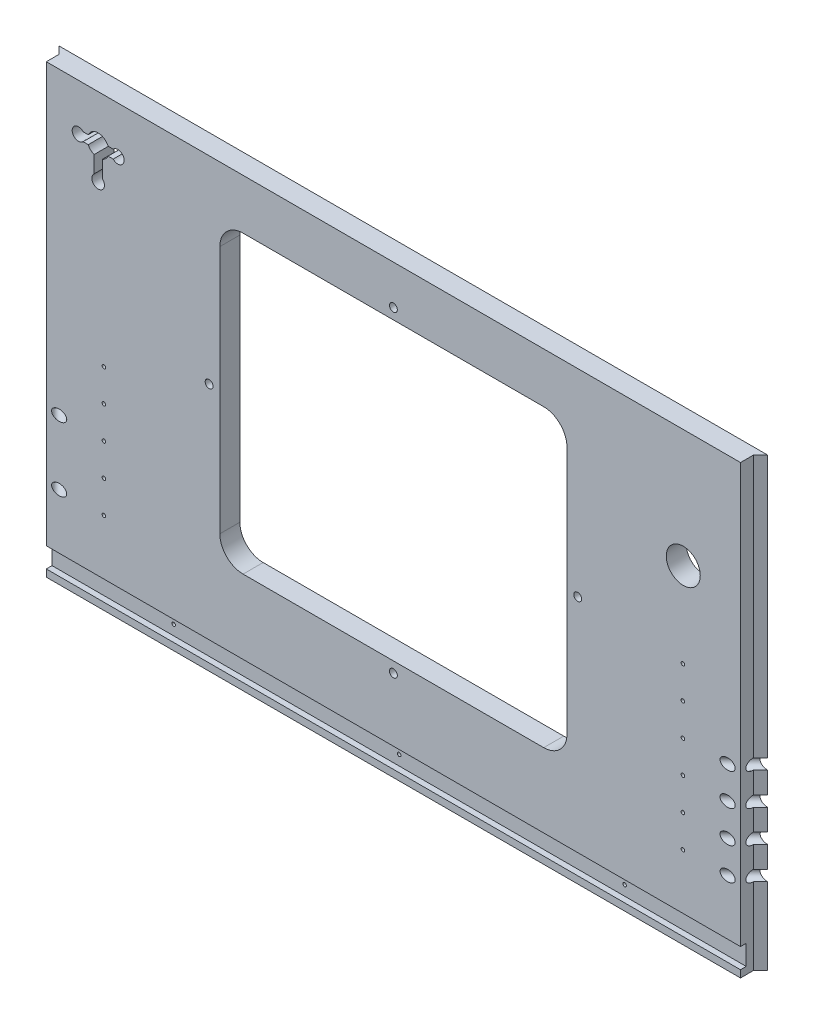
SolidWorks part; units mm, degrees
material "Maple"
ref_plane "Front Plane" through (0, 0, 0) normal (0, 0, 1) x (1, 0, 0)
ref_plane "Top Plane" through (0, 0, 0) normal (0, 1, 0) x (1, 0, 0)
ref_plane "Right Plane" through (0, 0, 0) normal (1, 0, 0) x (0, 0, -1)
sketch "Sketch1" plane through (0, 0, 0) normal (0, 0, 1) x (1, 0, 0)
  line L0 (8932.6508, -5243.5125) -> (10226.1458, -5243.5125)
  line L1 (9086.3208, -4722.0918) -> (10222.9708, -4853.7812)
  line L2 (8914.8708, -6342.0625) -> (10197.5708, -6342.0625)
  line L3 (8914.8708, -5808.6625) -> (10197.5708, -5808.6625)
  line L4 (8919.6333, -5253.0375) -> (10218.2083, -5253.0375)
  line L5 (9134.2633, -4656.1375) -> (9134.2633, -4638.3575)
  line L6 (9091.0833, -4638.3575) -> (9134.2633, -4638.3575)
  line L7 (9091.0833, -4567.2375) -> (9091.0833, -4638.3575)
  line L8 (9134.2633, -4656.1375) -> (9581.3033, -4656.1375)
  line L9 (9091.0833, -4567.2375) -> (9624.4833, -4567.2375)
  line L10 (9581.3033, -4656.1375) -> (9581.3033, -4638.3575)
  line L11 (9581.3033, -4638.3575) -> (9624.4833, -4638.3575)
  line L12 (9624.4833, -4567.2375) -> (9624.4833, -4638.3575)
  line L13 (8932.6508, -5225.7325) -> (9344.9775, -5225.7325)
  line L14 (8932.6508, -5256.2125) -> (8932.6508, -5243.5125)
  line L15 (8911.6958, -5256.2125) -> (8932.6508, -5256.2125)
  line L16 (8914.8708, -4722.0918) -> (9086.3208, -4722.0918)
  line L17 (8911.6958, -4715.5913) -> (8932.6508, -4715.5913)
  line L18 (8914.8708, -6342.0625) -> (8914.8708, -5808.6625)
  line L19 (12082.9917, -4722.0918) -> (10946.3417, -4853.7812)
  line L20 (12236.6617, -5243.5125) -> (10943.1667, -5243.5125)
  line L21 (10951.1042, -5253.0375) -> (12249.6792, -5253.0375)
  line L22 (10838.3917, -5656.2625) -> (11308.2917, -5656.2625)
  line L23 (10838.3917, -5719.7625) -> (11308.2917, -5719.7625)
  line L24 (10838.3917, -5742.5368) -> (11308.2917, -5742.5368)
  line L25 (10806.6417, -6342.0625) -> (11340.0417, -6342.0625)
  line L26 (10803.4667, -6335.7125) -> (11343.2167, -6335.7125)
  line L27 (10803.4667, -6317.9325) -> (11343.2167, -6317.9325)
  line L28 (10943.1667, -5225.7325) -> (11376.4483, -5225.7325)
  line L29 (11506.7292, -4754.5625) -> (10806.6417, -4827.5875)
  line L30 (11506.7292, -4567.2375) -> (11506.7292, -4754.5625)
  line L31 (10806.6417, -4567.2375) -> (10806.6417, -4827.5875)
  line L32 (10806.6417, -4567.2375) -> (11506.7292, -4567.2375)
  line L33 (10235.6708, -6329.3625) -> (10245.1958, -6329.3625)
  line L34 (10245.1958, -6329.3625) -> (10254.7208, -6278.5625)
  line L35 (10302.3458, -6329.3625) -> (10311.8708, -6278.5625)
  line L36 (10302.3458, -6329.3625) -> (10292.8208, -6329.3625)
  line L37 (10245.1958, -5821.3625) -> (10254.7208, -5872.1625)
  line L38 (10235.6708, -5821.3625) -> (10245.1958, -5821.3625)
  line L39 (10292.8208, -5821.3625) -> (10302.3458, -5821.3625)
  line L40 (10302.3458, -5821.3625) -> (10311.8708, -5872.1625)
  line L41 (10235.6708, -5821.3625) -> (10235.6708, -6329.3625)
  line L42 (10254.7208, -5872.1625) -> (10254.7208, -6278.5625)
  line L43 (10311.8708, -5872.1625) -> (10311.8708, -6278.5625)
  line L44 (10292.8208, -5821.3625) -> (10292.8208, -6329.3625)
  line L45 (8932.6508, -5225.7325) -> (8932.6508, -4715.5913)
  line L46 (8911.6958, -4715.5913) -> (8911.6958, -5256.2125)
  line L47 (8914.8708, -5248.275) -> (8914.8708, -4722.0918)
  line L48 (8919.6333, -5253.0375) -> (8914.8708, -5248.275)
  line L49 (8914.8708, -5145.0875) -> (8937.426, -5145.0875)
  line L50 (8914.8708, -5202.2375) -> (8937.426, -5202.2375)
  line L51 (10838.3917, -5656.2625) -> (10838.3917, -5719.7625)
  line L52 (10832.0417, -5736.1868) -> (10856.1717, -5736.1868)
  line L53 (10806.6417, -6342.0625) -> (10806.6417, -5818.7368)
  line L54 (10832.0417, -5649.9125) -> (10856.1717, -5649.9125)
  line L55 (10832.0417, -5726.1125) -> (10856.1717, -5726.1125)
  line L56 (10806.6417, -5818.7368) -> (10833.9015, -5818.7368)
  line L57 (10832.0417, -5806.0442) -> (10851.6815, -5806.0442)
  line L58 (10856.1717, -5801.5541) -> (10856.1717, -5736.1868)
  line L59 (10838.3917, -5814.2467) -> (10838.3917, -5742.5368)
  line L60 (10832.0417, -5806.0442) -> (10832.0417, -5736.1868)
  line L61 (10803.4667, -6317.9325) -> (10803.4667, -6335.7125)
  line L62 (10197.5708, -5808.6625) -> (10197.5708, -6342.0625)
  line L63 (9762.3842, -6348.4125) -> (9762.3842, -5802.3125)
  line L64 (9780.1642, -6348.4125) -> (9762.3842, -6348.4125)
  line L65 (9780.1642, -5802.3125) -> (9780.1642, -6348.4125)
  line L66 (9762.3842, -5802.3125) -> (9780.1642, -5802.3125)
  line L67 (9332.2775, -6348.4125) -> (9332.2775, -5802.3125)
  line L68 (9332.2775, -6348.4125) -> (9350.0575, -6348.4125)
  line L69 (9350.0575, -5802.3125) -> (9350.0575, -6348.4125)
  line L70 (9332.2775, -5802.3125) -> (9350.0575, -5802.3125)
  line L71 (9993.8374, -6061.075) -> (9993.8374, -6045.2418)
  line L72 (9998.5999, -6065.8375) -> (10014.4331, -6065.8375)
  line L73 (9998.5999, -6084.8875) -> (10014.4331, -6084.8875)
  line L74 (9993.8374, -6105.4832) -> (9993.8374, -6089.65)
  line L75 (9974.7874, -6105.4832) -> (9974.7874, -6089.65)
  line L76 (9954.1917, -6084.8875) -> (9970.0249, -6084.8875)
  line L77 (9974.7874, -6061.075) -> (9974.7874, -6045.2418)
  line L78 (9954.1917, -6065.8375) -> (9970.0249, -6065.8375)
  line L79 (10793.9417, -6237.2875) -> (10816.4969, -6237.2875)
  line L80 (10793.9417, -6294.4375) -> (10816.4969, -6294.4375)
  line L81 (10856.1717, -5649.9125) -> (10856.1717, -5726.1125)
  line L82 (10832.0417, -5726.1125) -> (10832.0417, -5649.9125)
  line L83 (10226.1458, -5225.7325) -> (10226.1458, -5243.5125)
  line L84 (10205.1908, -5257.8) -> (10205.1908, -4844.2499)
  line L85 (10230.9083, -4844.2499) -> (10230.9083, -5257.8)
  line L86 (10205.1908, -5257.8) -> (10230.9083, -5257.8)
  line L87 (10205.1908, -4844.2499) -> (10230.9083, -4844.2499)
  line L88 (10946.3417, -5176.8375) -> (10968.8969, -5176.8375)
  line L89 (9349.4676, -5141.9125) -> (9358.2674, -5141.9125)
  line L90 (10946.3417, -5119.6875) -> (10968.8969, -5119.6875)
  line L91 (9929.011, -4660.9635) -> (10066.0807, -4660.9635)
  line L92 (9929.011, -4678.7435) -> (10066.0807, -4678.7435)
  line L93 (10943.1667, -5225.7325) -> (10943.1667, -5243.5125)
  line L94 (10946.3417, -5248.275) -> (10951.1042, -5253.0375)
  line L95 (10946.3417, -5257.8063) -> (10946.3417, -4849.0188)
  line L96 (10964.1217, -5257.8) -> (10964.1217, -4844.2499)
  line L97 (10938.4042, -4844.2499) -> (10938.4042, -5257.8)
  line L98 (10938.4042, -5257.8) -> (10964.1217, -5257.8)
  line L99 (10964.1217, -4844.2499) -> (10938.4042, -4844.2499)
  line L100 (10344.8908, -4560.8875) -> (10369.0208, -4560.8875)
  line L101 (10344.8908, -4560.8875) -> (10369.0208, -4560.8875)
  line L102 (10800.2917, -4560.8875) -> (10824.4217, -4560.8875)
  line L103 (10200.4156, -5119.6875) -> (10222.9708, -5119.6875)
  line L104 (10200.4156, -5176.8375) -> (10222.9708, -5176.8375)
  line L105 (9344.9775, -5146.4026) -> (9344.9775, -5225.7325)
  line L106 (10344.8908, -4560.8875) -> (10344.8908, -4833.9375)
  line L107 (9792.8642, -5225.7325) -> (9792.8642, -5146.4026)
  line L108 (9362.7575, -5225.7325) -> (9775.0842, -5225.7325)
  line L109 (9680.3633, -4761.8396) -> (9680.3633, -4559.9604)
  line L110 (9656.2333, -4559.9604) -> (9680.3633, -4559.9604)
  line L111 (9656.2333, -4761.8396) -> (9680.3633, -4761.8396)
  line L112 (9656.2333, -4761.8396) -> (9656.2333, -4559.9604)
  line L113 (9779.5743, -5141.9125) -> (9788.374, -5141.9125)
  line L114 (10070.5708, -4665.4536) -> (10070.5708, -4674.2534)
  line L115 (9924.5208, -4674.2534) -> (9924.5208, -4665.4536)
  line L116 (12127.4417, -6188.3925) -> (12205.5015, -6188.3925)
  line L117 (12209.9917, -6170.6125) -> (12209.9917, -6183.9024)
  line L118 (9792.8642, -5225.7325) -> (10226.1458, -5225.7325)
  line L119 (9662.5833, -4754.5625) -> (10362.6708, -4827.5875)
  line L120 (9662.5833, -4567.2375) -> (9662.5833, -4754.5625)
  line L121 (10362.6708, -4567.2375) -> (10362.6708, -4827.5875)
  line L122 (9662.5833, -4567.2375) -> (10362.6708, -4567.2375)
  line L123 (10824.4217, -4833.9375) -> (10800.2917, -4833.9375)
  line L124 (10800.2917, -4833.9375) -> (10800.2917, -4560.8875)
  line L125 (10824.4217, -4560.8875) -> (10824.4217, -4833.9375)
  line L126 (10344.8908, -4833.9375) -> (10369.0208, -4833.9375)
  line L127 (10369.0208, -4833.9375) -> (10369.0208, -4560.8875)
  line L128 (10222.9708, -5248.275) -> (10218.2083, -5253.0375)
  line L129 (10222.9708, -5257.8063) -> (10222.9708, -4849.0188)
  line L130 (11734.6544, -5701.375) -> (11739.2301, -5701.375)
  line L131 (9362.7575, -5225.7325) -> (9362.7575, -5146.4026)
  line L132 (9775.0842, -5146.4026) -> (9775.0842, -5225.7325)
  line L133 (11761.3864, -5701.375) -> (11756.8282, -5701.375)
  line L134 (11734.6544, -5693.755) -> (11739.2301, -5693.755)
  line L135 (11761.4039, -5693.755) -> (11756.8282, -5693.755)
  line L136 (11734.6544, -5701.375) -> (11739.2301, -5701.375)
  line L137 (11744.3462, -5721.3024) -> (11744.3462, -5706.4179)
  line L138 (11751.7122, -5721.3024) -> (11751.7122, -5706.4179)
  line L139 (11740.0917, -6170.6125) -> (11740.0917, -6183.9024)
  line L140 (11689.2917, -6188.3925) -> (11822.6417, -6188.3925)
  line L141 (11689.2917, -6348.4093) -> (11689.2917, -6164.2657)
  line L142 (11689.2917, -6164.2657) -> (11746.4417, -6164.2657)
  line L143 (11746.4417, -6164.2657) -> (11746.4417, -6188.3925)
  line L144 (11689.2917, -6164.2657) -> (11746.4417, -6164.2657)
  line L145 (11340.0417, -5818.7368) -> (11340.0417, -6342.0625)
  line L146 (11290.5117, -5726.1125) -> (11314.6417, -5726.1125)
  line L147 (11290.5117, -5649.9125) -> (11290.5117, -5726.1125)
  line L148 (11340.0417, -5818.7368) -> (11312.7818, -5818.7368)
  line L149 (11314.6417, -5806.0442) -> (11295.0018, -5806.0442)
  line L150 (11290.5117, -5801.5541) -> (11290.5117, -5736.1868)
  line L151 (11308.2917, -5814.2467) -> (11308.2917, -5742.5368)
  line L152 (11314.6417, -5806.0442) -> (11314.6417, -5736.1868)
  line L153 (11290.5117, -5736.1868) -> (11314.6417, -5736.1868)
  line L154 (11848.0417, -6267.1325) -> (11962.3417, -6267.1325)
  line L155 (11962.3417, -6267.1325) -> (11962.3417, -6203.6325)
  line L156 (11343.2167, -6317.9325) -> (11343.2167, -6335.7125)
  line L157 (11365.4417, -5656.2625) -> (11365.4417, -5719.7625)
  line L158 (11365.4417, -5656.2625) -> (11479.7417, -5656.2625)
  line L159 (11778.1917, -6071.3937) -> (11802.3217, -6071.3937)
  line L160 (11314.6417, -5726.1125) -> (11314.6417, -5649.9125)
  line L161 (11314.6417, -5649.9125) -> (11290.5117, -5649.9125)
  line L162 (11308.2917, -5719.7625) -> (11308.2917, -5656.2625)
  line L163 (11689.2917, -6348.4093) -> (11713.4217, -6348.4093)
  line L164 (12203.6417, -6164.2657) -> (12260.7917, -6164.2657)
  line L165 (11713.4217, -6348.4093) -> (11713.4217, -6164.2657)
  line L166 (11695.6417, -6342.0625) -> (11695.6417, -6170.6125)
  line L167 (11695.6417, -6048.5337) -> (11699.4517, -6052.3437)
  line L168 (11822.6417, -6292.5325) -> (11822.6417, -6188.3925)
  line L169 (11695.6417, -6342.0625) -> (11695.6417, -6170.6125)
  line L170 (11848.0417, -6203.6325) -> (11962.3417, -6203.6325)
  line L171 (11848.0417, -6203.6325) -> (11848.0417, -6267.1325)
  line L172 (11987.7417, -6267.1325) -> (11987.7417, -6203.6325)
  line L173 (11784.5417, -6077.7437) -> (11784.5417, -6141.2438)
  line L174 (11517.8417, -5656.2625) -> (11632.1417, -5656.2625)
  line L175 (11632.1417, -5656.2625) -> (11632.1417, -5719.7625)
  line L176 (11632.1417, -5719.7625) -> (11517.8417, -5719.7625)
  line L177 (11517.8417, -5719.7625) -> (11517.8417, -5656.2625)
  line L178 (11692.4667, -6028.2137) -> (11692.4667, -6045.9937)
  line L179 (11695.6417, -5979.3188) -> (11718.1969, -5979.3188)
  line L180 (11695.6417, -5922.1687) -> (11718.1969, -5922.1687)
  line L181 (11821.0415, -5722.9375) -> (11821.0415, -5943.6)
  line L182 (11687.7042, -5651.5) -> (11701.9917, -5651.5)
  line L183 (11687.7042, -5651.5) -> (11687.7042, -6055.5251)
  line L184 (11687.7042, -6055.5251) -> (11701.9917, -6055.5251)
  line L185 (11701.9917, -6055.5251) -> (11701.9917, -5651.5)
  line L186 (11695.6417, -6055.2013) -> (11695.6417, -5649.595)
  line L187 (11695.6417, -5656.2625) -> (11695.6417, -6048.5337)
  line L188 (11695.6417, -6170.6125) -> (11740.0917, -6170.6125)
  line L189 (12203.6417, -6164.2657) -> (12203.6417, -6188.3925)
  line L190 (12254.4417, -6342.0625) -> (12254.4417, -6170.6125)
  line L191 (12129.0419, -5943.6) -> (12129.0419, -5722.9375)
  line L192 (12254.4417, -6048.5337) -> (12250.6317, -6052.3437)
  line L193 (12257.6167, -6045.9937) -> (12257.6167, -6028.2137)
  line L194 (12248.0917, -5651.5) -> (12262.3792, -5651.5)
  line L195 (12262.3792, -5651.5) -> (12262.3792, -6055.5251)
  line L196 (12262.3792, -6055.5251) -> (12248.0917, -6055.5251)
  line L197 (12248.0917, -6055.5251) -> (12248.0917, -5651.5)
  line L198 (12254.4417, -6141.2438) -> (12254.4417, -6077.7437)
  line L199 (12236.6617, -6164.2657) -> (12260.7917, -6164.2657)
  line L200 (12102.0417, -6267.1325) -> (11987.7417, -6267.1325)
  line L201 (11330.1865, -6237.2875) -> (11352.7417, -6237.2875)
  line L202 (11330.1865, -6294.4375) -> (11352.7417, -6294.4375)
  line L203 (11474.6617, -5851.8425) -> (11492.4417, -5851.8425)
  line L204 (11474.6617, -5808.6625) -> (11474.6617, -5851.8425)
  line L205 (11403.5417, -5808.6625) -> (11474.6617, -5808.6625)
  line L206 (11492.4417, -5851.8425) -> (11492.4417, -6298.8825)
  line L207 (11403.5417, -6342.0625) -> (11403.5417, -5808.6625)
  line L208 (11474.6617, -6298.8825) -> (11492.4417, -6298.8825)
  line L209 (11474.6617, -6342.0625) -> (11474.6617, -6298.8825)
  line L210 (11403.5417, -6342.0625) -> (11474.6617, -6342.0625)
  line L211 (11619.4417, -5851.8425) -> (11601.6617, -5851.8425)
  line L212 (11601.6617, -5808.6625) -> (11601.6617, -5851.8425)
  line L213 (11530.5417, -5808.6625) -> (11601.6617, -5808.6625)
  line L214 (11619.4417, -5851.8425) -> (11619.4417, -6298.8825)
  line L215 (11530.5417, -6342.0625) -> (11530.5417, -5808.6625)
  line L216 (11619.4417, -6298.8825) -> (11601.6617, -6298.8825)
  line L217 (11601.6617, -6342.0625) -> (11601.6617, -6298.8825)
  line L218 (11530.5417, -6342.0625) -> (11601.6617, -6342.0625)
  line L219 (11479.7417, -5719.7625) -> (11479.7417, -5656.2625)
  line L220 (11365.4417, -5719.7625) -> (11479.7417, -5719.7625)
  line L221 (11778.1917, -6147.5937) -> (11802.3217, -6147.5937)
  line L222 (11802.3217, -6071.3937) -> (11802.3217, -6147.5937)
  line L223 (11778.1917, -6147.5937) -> (11778.1917, -6071.3937)
  line L224 (12254.4417, -5922.1687) -> (12231.8865, -5922.1687)
  line L225 (12254.4417, -5979.3188) -> (12231.8865, -5979.3188)
  line L226 (12254.4417, -6055.2013) -> (12254.4417, -5649.595)
  line L227 (12254.4417, -6048.5337) -> (12254.4417, -5656.2625)
  line L228 (11841.6917, -5702.2873) -> (12108.3917, -5702.2873)
  line L229 (11822.6417, -6292.5325) -> (12127.4417, -6292.5325)
  line L230 (12127.4417, -6292.5325) -> (12127.4417, -6188.3925)
  line L231 (12254.4417, -6170.6125) -> (12209.9917, -6170.6125)
  line L232 (11695.6417, -6342.0625) -> (12254.4417, -6342.0625)
  line L233 (12236.6617, -6348.4093) -> (12260.7917, -6348.4093)
  line L234 (12260.7917, -6348.4093) -> (12260.7917, -6164.2657)
  line L235 (12236.6617, -6348.4093) -> (12236.6617, -6164.2657)
  line L236 (12102.0417, -6203.6325) -> (12102.0417, -6267.1325)
  line L237 (11987.7417, -6203.6325) -> (12102.0417, -6203.6325)
  line L238 (12236.6617, -6147.5937) -> (12236.6617, -6071.3937)
  line L239 (12203.6417, -6188.3925) -> (12260.7917, -6188.3925)
  line L240 (11098.7417, -4665.4536) -> (11098.7417, -4674.2534)
  line L241 (11394.2283, -5146.4026) -> (11394.2283, -5225.7325)
  line L242 (11376.4483, -5225.7325) -> (11376.4483, -5146.4026)
  line L243 (11394.2283, -5225.7325) -> (11806.555, -5225.7325)
  line L244 (11841.6917, -5964.2502) -> (12108.3917, -5964.2502)
  line L245 (12236.6617, -6147.5937) -> (12260.7917, -6147.5937)
  line L246 (12236.6617, -5256.2125) -> (12236.6617, -5243.5125)
  line L247 (12260.7917, -6147.5937) -> (12260.7917, -6071.3937)
  line L248 (12260.7917, -6071.3937) -> (12236.6617, -6071.3937)
  line L249 (12254.4417, -6077.7437) -> (11784.5417, -6077.7437)
  line L250 (11784.5417, -6141.2438) -> (12254.4417, -6141.2438)
  line L252 (12254.4417, -5656.2625) -> (11695.6417, -5656.2625)
  line L253 (11699.4517, -6052.3437) -> (12250.6317, -6052.3437)
  line L254 (11692.4667, -6045.9937) -> (12257.6167, -6045.9937)
  line L255 (11692.4667, -6028.2137) -> (12257.6167, -6028.2137)
  line L256 (11824.335, -5146.4026) -> (11824.335, -5225.7325)
  line L257 (11811.0451, -5141.9125) -> (11819.8449, -5141.9125)
  line L258 (11244.7917, -4674.2534) -> (11244.7917, -4665.4536)
  line L259 (11806.555, -5225.7325) -> (11806.555, -5146.4026)
  line L260 (11488.9492, -4761.8396) -> (11488.9492, -4559.9604)
  line L261 (11488.9492, -4559.9604) -> (11513.0792, -4559.9604)
  line L262 (11488.9492, -4761.8396) -> (11513.0792, -4761.8396)
  line L263 (11513.0792, -4761.8396) -> (11513.0792, -4559.9604)
  line L264 (11240.3015, -4660.9635) -> (11103.2318, -4660.9635)
  line L265 (11103.2318, -4678.7435) -> (11240.3015, -4678.7435)
  line L266 (12236.6617, -5225.7325) -> (12236.6617, -4715.5913)
  line L267 (12257.6167, -4715.5913) -> (12257.6167, -5256.2125)
  line L268 (12254.4417, -5248.275) -> (12254.4417, -4722.0918)
  line L269 (12236.6617, -5225.7325) -> (11824.335, -5225.7325)
  line L270 (12035.0492, -4656.1375) -> (12035.0492, -4638.3575)
  line L271 (12078.2292, -4638.3575) -> (12035.0492, -4638.3575)
  line L272 (12078.2292, -4567.2375) -> (12078.2292, -4638.3575)
  line L273 (12035.0492, -4656.1375) -> (11588.0092, -4656.1375)
  line L274 (11544.8292, -4567.2375) -> (12078.2292, -4567.2375)
  line L275 (11588.0092, -4656.1375) -> (11588.0092, -4638.3575)
  line L276 (11544.8292, -4638.3575) -> (11588.0092, -4638.3575)
  line L277 (11544.8292, -4567.2375) -> (11544.8292, -4638.3575)
  line L278 (12249.6792, -5253.0375) -> (12254.4417, -5248.275)
  line L280 (12257.6167, -5256.2125) -> (12236.6617, -5256.2125)
  line L281 (12231.8865, -5145.0875) -> (12254.4417, -5145.0875)
  line L282 (12231.8865, -5202.2375) -> (12254.4417, -5202.2375)
  line L283 (12236.6617, -4715.5913) -> (12257.6167, -4715.5913)
  line L284 (12082.9917, -4722.0918) -> (12254.4417, -4722.0918)
  line L285 (11380.9385, -5141.9125) -> (11389.7382, -5141.9125)
  circle A0 centre (8923.7608, -4778.9042) radius 1.5875
  circle A1 centre (9062.6598, -4736.3765) radius 2.3685
  circle A2 centre (9051.3958, -6281.7375) radius 22.225
  circle A3 centre (9083.1458, -6249.9875) radius 1.5875
  circle A4 centre (9083.1458, -6313.4875) radius 1.5875
  circle A5 centre (9019.6458, -6249.9875) radius 1.5875
  circle A6 centre (9019.6458, -6313.4875) radius 1.5875
  circle A7 centre (8972.3383, -5202.2375) radius 1.5875
  circle A8 centre (8923.7608, -5015.9708) radius 1.5875
  circle A9 centre (8923.7608, -5134.5042) radius 1.5875
  circle A10 centre (9054.5708, -5234.6225) radius 1.5875
  circle A11 centre (8923.7608, -4897.4375) radius 1.5875
  circle A12 centre (8972.3383, -5087.9375) radius 1.5875
  circle A13 centre (8972.3383, -5145.0875) radius 1.5875
  circle A14 centre (10847.2817, -5668.9625) radius 1.5875
  circle A15 centre (10847.2817, -5707.0625) radius 1.5875
  circle A16 centre (10847.2817, -5755.2368) radius 1.5875
  circle A17 centre (10851.4092, -6237.2875) radius 1.5875
  circle A18 centre (10851.4092, -6294.4375) radius 1.5875
  circle A19 centre (10847.2817, -5793.3442) radius 1.5875
  arc A20 (10833.9015, -5818.7368) -> (10838.3917, -5814.2467) centre (10836.1466, -5816.4918) ccw
  arc A21 (10851.6815, -5806.0442) -> (10856.1717, -5801.5541) centre (10853.9266, -5803.7992) ccw
  circle A22 centre (10882.8417, -6040.4375) radius 1.5875
  circle A23 centre (10882.8417, -6218.2375) radius 1.5875
  circle A24 centre (10882.8417, -5862.6375) radius 1.5875
  circle A25 centre (10908.2417, -6326.8225) radius 1.5875
  circle A26 centre (10908.2417, -6326.8225) radius 1.5875
  circle A27 centre (10851.4092, -6180.1375) radius 1.5875
  circle A28 centre (10815.5317, -4783.4231) radius 1.5875
  circle A29 centre (10815.5317, -4696.9488) radius 1.5875
  circle A30 centre (10815.5317, -4610.4746) radius 1.5875
  circle A31 centre (10979.1323, -4867.0082) radius 2.3685
  circle A32 centre (10190.1802, -4867.0082) radius 2.3685
  circle A33 centre (10955.2317, -4929.9812) radius 1.5875
  circle A34 centre (10955.2317, -5031.5812) radius 1.5875
  circle A35 centre (10214.0808, -4929.9812) radius 1.5875
  circle A36 centre (10214.0808, -5031.5812) radius 1.5875
  circle A37 centre (9341.1675, -6265.8625) radius 1.5875
  circle A38 centre (9771.2742, -5884.8625) radius 1.5875
  circle A39 centre (9771.2742, -6138.8625) radius 1.5875
  circle A40 centre (9771.2742, -6011.8625) radius 1.5875
  arc A41 (10036.2287, -6113.8083) -> (10051.3426, -6111.6033) centre (10042.9639, -6107.0732) ccw
  arc A42 (10051.3426, -6111.6033) -> (10051.3426, -6039.1217) centre (9984.3124, -6075.3625) ccw
  arc A43 (10051.3426, -6039.1217) -> (10036.2287, -6036.9167) centre (10042.9639, -6043.6518) ccw
  arc A44 (10034.5851, -6102.5431) -> (10034.5851, -6048.1819) centre (9984.3124, -6075.3625) ccw
  arc A45 (10034.5851, -6102.5431) -> (10036.2287, -6113.8083) centre (10042.9639, -6107.0732) ccw
  arc A46 (10036.2287, -6036.9167) -> (10034.5851, -6048.1819) centre (10042.9639, -6043.6518) ccw
  arc A47 (9945.8666, -6127.2787) -> (9948.0717, -6142.3927) centre (9952.6018, -6134.0139) ccw
  arc A48 (9948.0717, -6142.3927) -> (10020.5532, -6142.3927) centre (9984.3124, -6075.3625) ccw
  arc A49 (10020.5532, -6142.3927) -> (10022.7583, -6127.2787) centre (10016.0231, -6134.0139) ccw
  arc A50 (9957.1319, -6125.6352) -> (10011.493, -6125.6352) centre (9984.3124, -6075.3625) ccw
  arc A51 (9957.1319, -6125.6352) -> (9945.8666, -6127.2787) centre (9952.6018, -6134.0139) ccw
  arc A52 (10022.7583, -6127.2787) -> (10011.493, -6125.6352) centre (10016.0231, -6134.0139) ccw
  arc A53 (9932.3962, -6036.9167) -> (9917.2822, -6039.1217) centre (9925.661, -6043.6518) ccw
  arc A54 (9917.2822, -6039.1217) -> (9917.2822, -6111.6033) centre (9984.3124, -6075.3625) ccw
  arc A55 (9917.2822, -6111.6033) -> (9932.3962, -6113.8083) centre (9925.661, -6107.0732) ccw
  arc A56 (9934.0398, -6048.1819) -> (9934.0398, -6102.5431) centre (9984.3124, -6075.3625) ccw
  arc A57 (9934.0398, -6048.1819) -> (9932.3962, -6036.9167) centre (9925.661, -6043.6518) ccw
  arc A58 (9932.3962, -6113.8083) -> (9934.0398, -6102.5431) centre (9925.661, -6107.0732) ccw
  arc A59 (9945.8666, -6023.4463) -> (9957.1319, -6025.0898) centre (9952.6018, -6016.7111) ccw
  arc A60 (10011.493, -6025.0898) -> (10022.7583, -6023.4463) centre (10016.0231, -6016.7111) ccw
  arc A61 (10011.493, -6025.0898) -> (9957.1319, -6025.0898) centre (9984.3124, -6075.3625) ccw
  arc A62 (9948.0717, -6008.3323) -> (9945.8666, -6023.4463) centre (9952.6018, -6016.7111) ccw
  arc A63 (10020.5532, -6008.3323) -> (9948.0717, -6008.3323) centre (9984.3124, -6075.3625) ccw
  arc A64 (10022.7583, -6023.4463) -> (10020.5532, -6008.3323) centre (10016.0231, -6016.7111) ccw
  arc A65 (10005.0943, -6187.7574) -> (10096.7073, -6096.1443) centre (9984.3124, -6075.3625) ccw
  arc A66 (9993.8374, -6178.3911) -> (10005.0943, -6187.7574) centre (10003.3624, -6178.3911) ccw
  arc A67 (10001.6306, -6169.0249) -> (10077.9748, -6092.6807) centre (9984.3124, -6075.3625) ccw
  arc A68 (10087.3411, -6084.8875) -> (10077.9748, -6092.6807) centre (10087.3411, -6094.4125) ccw
  arc A69 (10001.6306, -6169.0249) -> (9993.8374, -6178.3911) centre (10003.3624, -6178.3911) ccw
  arc A70 (9963.5306, -6187.7574) -> (9974.7874, -6178.3911) centre (9965.2624, -6178.3911) ccw
  arc A71 (9871.9176, -6096.1443) -> (9963.5306, -6187.7574) centre (9984.3124, -6075.3625) ccw
  arc A72 (9881.2838, -6084.8875) -> (9871.9176, -6096.1443) centre (9881.2838, -6094.4125) ccw
  arc A73 (9890.65, -6092.6807) -> (9966.9943, -6169.0249) centre (9984.3124, -6075.3625) ccw
  arc A74 (9974.7874, -6178.3911) -> (9966.9943, -6169.0249) centre (9965.2624, -6178.3911) ccw
  arc A75 (9890.65, -6092.6807) -> (9881.2838, -6084.8875) centre (9881.2838, -6094.4125) ccw
  arc A76 (9871.9176, -6054.5807) -> (9881.2838, -6065.8375) centre (9881.2838, -6056.3125) ccw
  arc A77 (9963.5306, -5962.9676) -> (9871.9176, -6054.5807) centre (9984.3124, -6075.3625) ccw
  arc A78 (9974.7874, -5972.3339) -> (9963.5306, -5962.9676) centre (9965.2624, -5972.3339) ccw
  arc A79 (9966.9943, -5981.7001) -> (9890.65, -6058.0443) centre (9984.3124, -6075.3625) ccw
  arc A80 (9881.2838, -6065.8375) -> (9890.65, -6058.0443) centre (9881.2838, -6056.3125) ccw
  arc A81 (9966.9943, -5981.7001) -> (9974.7874, -5972.3339) centre (9965.2624, -5972.3339) ccw
  arc A82 (10077.9748, -6058.0443) -> (10087.3411, -6065.8375) centre (10087.3411, -6056.3125) ccw
  arc A83 (9993.8374, -5972.3339) -> (10001.6306, -5981.7001) centre (10003.3624, -5972.3339) ccw
  arc A84 (10077.9748, -6058.0443) -> (10001.6306, -5981.7001) centre (9984.3124, -6075.3625) ccw
  arc A85 (10087.3411, -6065.8375) -> (10096.7073, -6054.5807) centre (10087.3411, -6056.3125) ccw
  arc A86 (10096.7073, -6054.5807) -> (10005.0943, -5962.9676) centre (9984.3124, -6075.3625) ccw
  arc A87 (10005.0943, -5962.9676) -> (9993.8374, -5972.3339) centre (10003.3624, -5972.3339) ccw
  arc A88 (10014.4331, -6065.8375) -> (10018.7361, -6059.0339) centre (10014.4331, -6061.075) ccw
  arc A89 (10018.7361, -6059.0339) -> (10000.641, -6040.9388) centre (9984.3124, -6075.3625) ccw
  arc A90 (10000.641, -6040.9388) -> (9993.8374, -6045.2418) centre (9998.5999, -6045.2418) ccw
  arc A91 (9993.8374, -6061.075) -> (9998.5999, -6065.8375) centre (9998.5999, -6061.075) ccw
  arc A92 (9993.8374, -6105.4832) -> (10000.641, -6109.7862) centre (9998.5999, -6105.4832) ccw
  arc A93 (10000.641, -6109.7862) -> (10018.7361, -6091.6911) centre (9984.3124, -6075.3625) ccw
  arc A94 (10018.7361, -6091.6911) -> (10014.4331, -6084.8875) centre (10014.4331, -6089.65) ccw
  arc A95 (9998.5999, -6084.8875) -> (9993.8374, -6089.65) centre (9998.5999, -6089.65) ccw
  arc A96 (9954.1917, -6084.8875) -> (9949.8888, -6091.6911) centre (9954.1917, -6089.65) ccw
  arc A97 (9949.8888, -6091.6911) -> (9967.9839, -6109.7862) centre (9984.3124, -6075.3625) ccw
  arc A98 (9967.9839, -6109.7862) -> (9974.7874, -6105.4832) centre (9970.0249, -6105.4832) ccw
  arc A99 (9974.7874, -6089.65) -> (9970.0249, -6084.8875) centre (9970.0249, -6089.65) ccw
  arc A100 (9970.0249, -6065.8375) -> (9974.7874, -6061.075) centre (9970.0249, -6061.075) ccw
  arc A101 (9949.8888, -6059.0339) -> (9954.1917, -6065.8375) centre (9954.1917, -6061.075) ccw
  arc A102 (9967.9839, -6040.9388) -> (9949.8888, -6059.0339) centre (9984.3124, -6075.3625) ccw
  arc A103 (9974.7874, -6045.2418) -> (9967.9839, -6040.9388) centre (9970.0249, -6045.2418) ccw
  arc A104 (10096.7073, -6096.1443) -> (10087.3411, -6084.8875) centre (10087.3411, -6094.4125) ccw
  circle A105 centre (9771.2742, -6265.8625) radius 1.5875
  circle A106 centre (9341.1675, -5884.8625) radius 1.5875
  circle A107 centre (9341.1675, -6138.8625) radius 1.5875
  circle A108 centre (9341.1675, -6011.8625) radius 1.5875
  circle A109 centre (11037.2315, -4887.5494) radius 15.0812
  arc A110 (9349.4676, -5141.9125) -> (9344.9775, -5146.4026) centre (9347.2226, -5144.1576) ccw
  arc A111 (9362.7575, -5146.4026) -> (9358.2674, -5141.9125) centre (9360.5124, -5144.1576) ccw
  circle A112 centre (9946.7458, -4669.8535) radius 1.5875
  arc A113 (9924.5208, -4674.2534) -> (9929.011, -4678.7435) centre (9926.7659, -4676.4984) ccw
  circle A114 centre (11003.8092, -5176.8375) radius 1.5875
  circle A115 centre (11003.8092, -5119.6875) radius 1.5875
  circle A116 centre (10353.7808, -4696.9488) radius 1.5875
  circle A117 centre (10353.7808, -4610.4746) radius 1.5875
  circle A118 centre (10353.7808, -4783.4231) radius 1.5875
  circle A119 centre (11003.8092, -5062.5375) radius 1.5875
  circle A120 centre (9353.8675, -5160.9625) radius 1.5875
  circle A121 centre (9638.7708, -5234.6225) radius 1.5875
  circle A122 centre (9671.4733, -4724.1144) radius 1.5875
  circle A123 centre (9671.4733, -4661.3637) radius 1.5875
  circle A124 centre (9671.4733, -4598.6129) radius 1.5875
  arc A125 (9792.8642, -5146.4026) -> (9788.374, -5141.9125) centre (9790.6191, -5144.1576) ccw
  arc A126 (9779.5743, -5141.9125) -> (9775.0842, -5146.4026) centre (9777.3292, -5144.1576) ccw
  circle A127 centre (10048.3458, -4669.8535) radius 1.5875
  arc A128 (10070.5708, -4665.4536) -> (10066.0807, -4660.9635) centre (10068.3258, -4663.2086) ccw
  arc A129 (10066.0807, -4678.7435) -> (10070.5708, -4674.2534) centre (10068.3258, -4676.4984) ccw
  circle A130 centre (9997.5458, -4669.8535) radius 1.5875
  arc A131 (9929.011, -4660.9635) -> (9924.5208, -4665.4536) centre (9926.7659, -4663.2086) ccw
  circle A132 centre (10132.081, -4887.5494) radius 15.0812
  circle A133 centre (10165.5033, -5176.8375) radius 1.5875
  circle A134 centre (10165.5033, -5119.6875) radius 1.5875
  circle A135 centre (9486.3708, -5234.6225) radius 1.5875
  circle A136 centre (10165.5033, -5062.5375) radius 1.5875
  circle A137 centre (9206.9708, -5234.6225) radius 1.5875
  circle A138 centre (10070.5708, -5234.6225) radius 1.5875
  circle A139 centre (9918.1708, -5234.6225) radius 1.5875
  circle A140 centre (9783.9742, -5160.9625) radius 1.5875
  circle A141 centre (9783.9742, -5193.9825) radius 1.5875
  circle A142 centre (9353.8675, -5193.9825) radius 1.5875
  circle A143 centre (11073.3417, -6326.8225) radius 1.5875
  circle A144 centre (11073.3417, -6326.8225) radius 1.5875
  circle A145 centre (11295.2742, -6180.1375) radius 1.5875
  circle A146 centre (11295.2742, -6294.4375) radius 1.5875
  circle A147 centre (11295.2742, -6237.2875) radius 1.5875
  circle A148 centre (11975.0417, -5692.775) radius 3.4925
  circle A149 centre (11263.8417, -5862.6375) radius 1.5875
  arc A150 (11739.2301, -5701.375) -> (11744.3462, -5706.4179) centre (11748.0292, -5697.565) ccw
  arc A151 (11751.7122, -5706.4179) -> (11756.8282, -5701.375) centre (11748.0292, -5697.565) ccw
  arc A152 (11744.3462, -5721.3024) -> (11751.7122, -5721.3024) centre (11748.0292, -5725.505) ccw
  arc A153 (11734.6544, -5693.755) -> (11724.9787, -5697.565) centre (11730.5667, -5697.565) ccw
  arc A154 (11756.8282, -5693.755) -> (11739.2301, -5693.755) centre (11748.0292, -5697.565) ccw
  arc A155 (11724.9787, -5697.565) -> (11734.6544, -5701.375) centre (11730.5667, -5697.565) ccw
  arc A156 (11761.3864, -5701.375) -> (11771.0797, -5697.565) centre (11765.4842, -5697.565) ccw
  arc A157 (11771.0797, -5697.565) -> (11761.4039, -5693.755) centre (11765.4917, -5697.565) ccw
  arc A158 (11740.0917, -6183.9024) -> (11744.5818, -6188.3925) centre (11742.3367, -6186.1474) ccw
  arc A159 (12205.5015, -6188.3925) -> (12209.9917, -6183.9024) centre (12207.7466, -6186.1474) ccw
  circle A160 centre (11299.4017, -5793.3442) radius 1.5875
  arc A161 (11308.2917, -5814.2467) -> (11312.7818, -5818.7368) centre (11310.5367, -5816.4918) ccw
  arc A162 (11290.5117, -5801.5541) -> (11295.0018, -5806.0442) centre (11292.7567, -5803.7992) ccw
  circle A163 centre (11704.5317, -6314.149) radius 1.5875
  circle A164 centre (11748.9817, -6208.7125) radius 1.5875
  circle A165 centre (11263.8417, -6218.2375) radius 1.5875
  circle A166 centre (11263.8417, -6040.4375) radius 1.5875
  circle A167 centre (11238.4417, -6326.8225) radius 1.5875
  circle A168 centre (11238.4417, -6326.8225) radius 1.5875
  circle A169 centre (11299.4017, -5668.9625) radius 1.5875
  circle A170 centre (11299.4017, -5707.0625) radius 1.5875
  circle A171 centre (11726.7567, -6179.5025) radius 1.5875
  circle A172 centre (11704.5317, -6199.3198) radius 1.5875
  circle A173 centre (11748.9817, -6272.2125) radius 1.5875
  circle A174 centre (11704.5317, -6256.7344) radius 1.5875
  circle A175 centre (11299.4017, -5755.2368) radius 1.5875
  circle A176 centre (11913.4467, -6301.4225) radius 1.5875
  circle A177 centre (11790.2567, -6301.4225) radius 1.5875
  circle A178 centre (11793.4317, -6128.5437) radius 1.5875
  circle A179 centre (11753.1092, -5865.0188) radius 1.5875
  circle A180 centre (11809.9417, -6037.1038) radius 1.5875
  circle A181 centre (11809.9417, -6037.1038) radius 1.5875
  circle A182 centre (11753.1092, -5922.1687) radius 1.5875
  circle A183 centre (11975.0417, -5973.7625) radius 3.4925
  circle A184 centre (11975.0417, -6037.1038) radius 1.5875
  circle A185 centre (11753.1092, -5979.3188) radius 1.5875
  circle A186 centre (11975.0417, -6037.1038) radius 1.5875
  arc A187 (11841.6917, -5702.2873) -> (11821.0415, -5722.9375) centre (11841.6917, -5722.9375) ccw
  circle A188 centre (11811.5292, -5833.2687) radius 3.4925
  arc A189 (11821.0415, -5943.6) -> (11841.6917, -5964.2502) centre (11841.6917, -5943.6) ccw
  circle A190 centre (12196.9742, -5865.0188) radius 1.5875
  arc A191 (12129.0419, -5722.9375) -> (12108.3917, -5702.2873) centre (12108.3917, -5722.9375) ccw
  circle A192 centre (12036.6367, -6301.4225) radius 1.5875
  circle A193 centre (12159.8267, -6301.4225) radius 1.5875
  circle A194 centre (12138.5542, -5833.2687) radius 3.4925
  circle A195 centre (12197.2917, -5761.0375) radius 15.0812
  circle A196 centre (11793.4317, -6090.4437) radius 1.5875
  circle A197 centre (12196.9742, -5922.1687) radius 1.5875
  arc A198 (12108.3917, -5964.2502) -> (12129.0419, -5943.6) centre (12108.3917, -5943.6) ccw
  circle A199 centre (12196.9742, -5979.3188) radius 1.5875
  circle A200 centre (12201.1017, -6272.2125) radius 1.5875
  circle A201 centre (12245.5517, -6314.149) radius 1.5875
  circle A202 centre (12245.5517, -6256.7344) radius 1.5875
  circle A203 centre (12201.1017, -6208.7125) radius 1.5875
  circle A204 centre (12223.3267, -6179.5025) radius 1.5875
  circle A205 centre (12245.5517, -6199.3198) radius 1.5875
  circle A206 centre (11171.7667, -4669.8535) radius 1.5875
  circle A207 centre (11222.5667, -4669.8535) radius 1.5875
  arc A208 (11240.3015, -4678.7435) -> (11244.7917, -4674.2534) centre (11242.5466, -4676.4984) ccw
  circle A209 centre (11385.3383, -5193.9825) radius 1.5875
  circle A210 centre (12106.6527, -4736.3765) radius 2.3685
  circle A211 centre (12140.1417, -6037.1038) radius 1.5875
  circle A212 centre (12140.1417, -6037.1038) radius 1.5875
  circle A213 centre (12245.5517, -6090.4437) radius 1.5875
  circle A214 centre (12245.5517, -6128.5437) radius 1.5875
  circle A215 centre (11385.3383, -5160.9625) radius 1.5875
  arc A216 (11824.335, -5146.4026) -> (11819.8449, -5141.9125) centre (11822.0899, -5144.1576) ccw
  arc A217 (11811.0451, -5141.9125) -> (11806.555, -5146.4026) centre (11808.8001, -5144.1576) ccw
  circle A218 centre (11815.445, -5193.9825) radius 1.5875
  circle A219 centre (11815.445, -5160.9625) radius 1.5875
  circle A220 centre (11530.5417, -5234.6225) radius 1.5875
  circle A221 centre (11962.3417, -5234.6225) radius 1.5875
  arc A222 (11244.7917, -4665.4536) -> (11240.3015, -4660.9635) centre (11242.5466, -4663.2086) ccw
  circle A223 centre (11682.9417, -5234.6225) radius 1.5875
  circle A224 centre (11497.8392, -4724.1144) radius 1.5875
  circle A225 centre (11497.8392, -4661.3637) radius 1.5875
  circle A226 centre (11497.8392, -4598.6129) radius 1.5875
  circle A227 centre (11120.9667, -4669.8535) radius 1.5875
  arc A228 (11103.2318, -4660.9635) -> (11098.7417, -4665.4536) centre (11100.9867, -4663.2086) ccw
  arc A229 (11098.7417, -4674.2534) -> (11103.2318, -4678.7435) centre (11100.9867, -4676.4984) ccw
  circle A230 centre (12196.9742, -5202.2375) radius 1.5875
  circle A231 centre (12245.5517, -5015.9708) radius 1.5875
  circle A232 centre (12245.5517, -5134.5042) radius 1.5875
  circle A233 centre (12114.7417, -5234.6225) radius 1.5875
  circle A234 centre (12245.5517, -4897.4375) radius 1.5875
  circle A235 centre (12245.5517, -4778.9042) radius 1.5875
  circle A236 centre (12196.9742, -5087.9375) radius 1.5875
  circle A237 centre (12196.9742, -5145.0875) radius 1.5875
  circle A238 centre (11098.7417, -5234.6225) radius 1.5875
  circle A239 centre (11251.1417, -5234.6225) radius 1.5875
  arc A240 (11380.9385, -5141.9125) -> (11376.4483, -5146.4026) centre (11378.6934, -5144.1576) ccw
  arc A241 (11394.2283, -5146.4026) -> (11389.7382, -5141.9125) centre (11391.9833, -5144.1576) ccw
sketch "CabFrontOutline" plane through (0, 0, 0) normal (0, 0, 1) x (1, 0, 0)
  line L0 (11695.6417, -6055.2013) -> (11695.6417, -5649.595) construction
  line L1 (11695.6417, -6052.3437) -> (12324.2917, -6052.3437)
  line L3 (12324.2917, -6052.3437) -> (12324.2917, -5656.2625)
  line L4 (12324.2917, -5656.2625) -> (11695.6417, -5656.2625)
  line L5 (11695.6417, -5656.2625) -> (11695.6417, -6052.3437)
  point P1 (0, 0)
  point P2 (0, 0)
  dimension "CabFrontWidth" = 628.65
extrude "CabFront_Thickness" add sketch "CabFrontOutline" against normal blind 17.78
sketch "CabFront_CoinDoorCuts" plane through (0, 0, 0) normal (0, 0, 1) x (1, 0, 0)
  line L0 (11855.9665, -5700.6998) -> (12163.9669, -5700.6998)
  line L1 (12163.9669, -5700.6998) -> (12163.9669, -5962.6627)
  line L2 (12163.9669, -5962.6627) -> (11855.9665, -5962.6627)
  line L3 (11855.9665, -5962.6627) -> (11855.9665, -5700.6998)
  line L4 (11734.6544, -5693.755) -> (11739.2301, -5693.755)
  line L5 (11734.6544, -5701.375) -> (11739.2301, -5701.375)
  line L6 (11744.3462, -5706.4179) -> (11744.3462, -5721.3024)
  line L7 (11751.7122, -5706.4179) -> (11751.7122, -5721.3024)
  line L8 (11756.8282, -5701.375) -> (11761.3864, -5701.375)
  line L9 (11761.3864, -5693.755) -> (11756.8282, -5693.755)
  line L10 (11753.1092, -5865.0188) -> (11753.1092, -5922.1687) construction
  line L11 (11753.1092, -5922.1687) -> (11753.1092, -5979.3188) construction
  line L12 (11695.6417, -5656.2625) -> (11695.6417, -6052.3437) construction
  line L13 (12266.8242, -5865.0188) -> (12266.8242, -5922.1687) construction
  line L14 (12266.8242, -5922.1687) -> (12266.8242, -5979.3188) construction
  line L15 (12324.2917, -6052.3437) -> (12324.2917, -5656.2625) construction
  line L16 (11809.9417, -6037.1038) -> (12009.9667, -6037.1038) construction
  line L17 (12009.9667, -6037.1038) -> (12209.9917, -6037.1038) construction
  line L18 (12009.9667, -6037.1038) -> (12009.9667, -6052.3437) construction
  line L19 (11695.6417, -6052.3437) -> (12324.2917, -6052.3437) construction
  line L20 (12009.9667, -5691.1875) -> (12009.9667, -5700.6998) construction
  line L21 (11846.4542, -5831.6812) -> (11855.9665, -5831.6812) construction
  line L22 (12009.9667, -5972.175) -> (12009.9667, -5962.6627) construction
  line L23 (12173.4792, -5831.6812) -> (12163.9669, -5831.6812) construction
  line L24 (12009.9667, -5691.1875) -> (12009.9667, -5656.2625) construction
  line L25 (12324.2917, -5656.2625) -> (11695.6417, -5656.2625) construction
  circle A0 centre (11753.1092, -5893.5938) radius 1.5875
  circle A1 centre (11753.1092, -5950.7437) radius 1.5875
  circle A2 centre (12266.8242, -5893.5938) radius 1.5875
  circle A3 centre (12266.8242, -5950.7437) radius 1.5875
  arc A4 (11734.6544, -5693.755) -> (11734.6544, -5701.375) centre (11730.5667, -5697.565) ccw
  arc A5 (11724.9787, -5697.565) -> (11734.6544, -5701.375) centre (11730.5667, -5697.565) ccw construction
  arc A6 (11739.2301, -5693.755) -> (11756.8282, -5693.755) centre (11748.0292, -5697.565) cw
  arc A7 (11756.8282, -5693.755) -> (11739.2301, -5693.755) centre (11748.0292, -5697.565) ccw construction
  arc A8 (11744.3462, -5721.3024) -> (11751.7122, -5721.3024) centre (11748.0292, -5725.505) ccw
  arc A9 (11744.3462, -5721.3024) -> (11751.7122, -5721.3024) centre (11748.0292, -5725.505) ccw construction
  arc A10 (11739.2301, -5701.375) -> (11744.3462, -5706.4179) centre (11748.0292, -5697.565) ccw
  arc A11 (11739.2301, -5701.375) -> (11744.3462, -5706.4179) centre (11748.0292, -5697.565) ccw construction
  arc A12 (11751.7122, -5706.4179) -> (11756.8282, -5701.375) centre (11748.0292, -5697.565) ccw
  arc A13 (11751.7122, -5706.4179) -> (11756.8282, -5701.375) centre (11748.0292, -5697.565) ccw construction
  arc A14 (11761.3864, -5701.375) -> (11771.0797, -5697.565) centre (11765.4842, -5697.565) ccw
  circle A15 centre (12266.8242, -5836.4438) radius 1.5875
  arc A16 (11761.3864, -5701.375) -> (11771.0797, -5697.565) centre (11765.4842, -5697.565) ccw construction
  arc A17 (11771.0797, -5697.565) -> (11761.3864, -5693.755) centre (11765.4842, -5697.565) ccw
  circle A18 centre (12267.1417, -5761.0375) radius 15.0812
  circle A19 centre (12173.4792, -5831.6812) radius 3.4925
  circle A20 centre (12266.8242, -5865.0188) radius 1.5875
  circle A21 centre (12266.8242, -5922.1687) radius 1.5875
  circle A22 centre (12266.8242, -5979.3188) radius 1.5875
  circle A23 centre (12209.9917, -6037.1038) radius 1.5875
  circle A24 centre (12009.9667, -6037.1038) radius 1.5875
  circle A25 centre (11809.9417, -6037.1038) radius 1.5875
  circle A26 centre (11753.1092, -5979.3188) radius 1.5875
  circle A27 centre (11753.1092, -5922.1687) radius 1.5875
  circle A28 centre (11753.1092, -5865.0188) radius 1.5875
  circle A29 centre (11846.4542, -5831.6812) radius 3.4925
  circle A30 centre (12009.9667, -5972.175) radius 3.4925
  circle A31 centre (12009.9667, -5691.1875) radius 3.4925
  dimension "D1" = 57.4675
  dimension "D2" = 57.4675
  dimension "D3" = 57.15
  dimension "D4" = 34.925
  dimension "D5" = 308.0004
  dimension "D6" = 9.5123
  dimension "D7" = 261.9629
extrude "Cut-Extrude1" cut sketch "CabFront_CoinDoorCuts" against normal up to surface (17.78 mm away) up to face at (12009.9667, -5854.3031, -17.78)
sketch "CabFront_BottomLedge" plane through (0, 0, 0) normal (0, 0, 1) x (1, 0, 0)
  line L0 (11975.0417, -6028.2137) -> (11695.6417, -6028.2137)
  line L1 (11975.0417, -6028.2137) -> (11975.0417, -6052.3437) construction
  line L2 (11695.6417, -6055.2013) -> (11695.6417, -5649.595) construction
  line L3 (11692.4667, -6028.2137) -> (12257.6167, -6028.2137) construction
  line L4 (11699.4517, -6052.3437) -> (12250.6317, -6052.3437) construction
  line L5 (11695.6417, -6028.2137) -> (11695.6417, -6045.9937)
  line L6 (11695.6417, -6045.9937) -> (12324.2917, -6045.9937)
  line L7 (12324.2917, -6052.3437) -> (12324.2917, -5656.2625) construction
  line L9 (12324.2917, -6045.9937) -> (12324.2917, -6028.2137)
  line L10 (12324.2917, -6028.2137) -> (11975.0417, -6028.2137)
  dimension "D1" = 17.78
extrude "CabFrontBottomLedge_Depth" cut sketch "CabFront_BottomLedge" against normal blind 5.08
sketch "CabFront_EdgeBevel" plane through (0, -6052.3437, 0) normal (0, -1, 0) x (1, 0, 0)
  line L0 (11701.9917, -11.43) -> (11701.9917, 0)
  line L1 (11701.9917, 0) -> (11695.6417, 0)
  line L2 (11695.6417, 0) -> (11695.6417, -17.78)
  line L5 (12317.9417, -11.43) -> (12324.2917, -17.78)
  line L10 (11695.6417, -17.78) -> (11701.9917, -11.43)
  line L11 (12317.9417, -11.43) -> (12317.9417, 0)
  line L12 (11695.6417, 0) -> (12324.2917, 0) construction
  line L13 (12317.9417, 0) -> (12324.2917, 0)
  line L14 (12324.2917, 0) -> (12324.2917, -17.78)
  dimension "D1" = 6.35
  dimension "D2" = 6.35
  dimension "D3" = 6.35
  dimension "D4" = 6.35
extrude "Cut-Extrude4" cut sketch "CabFront_EdgeBevel" against normal up to surface (396.0813 mm away) up to face at (12009.9667, -5656.2625, -8.89)
fillet "Fillet1" radius 20.6502 4 edges at (11855.9665, -5700.6998, -8.89) (11855.9665, -5962.6627, -8.89) (12163.9669, -5962.6627, -8.89) (12163.9669, -5700.6998, -8.89)
sketch "Sketch2" plane through (5872.7944, 0, 5872.7944) normal (0.7071, 0, 0.7071) x (0.7071, 0, -0.7071)
  circle A0 centre (8282.6399, -5922.1688) radius 4.7625
  circle A1 centre (8282.6399, -5979.3188) radius 4.7625
extrude "Cut-Extrude5" cut sketch "Sketch2" against normal blind 76.2
sketch "Sketch3" plane through (6137.1723, 0, -6137.1723) normal (-0.7071, 0, 0.7071) x (0.7071, 0, 0.7071)
  circle A0 centre (8702.0179, -5922.1688) radius 4.7625
  circle A1 centre (8702.0179, -5979.3188) radius 4.7625
extrude "Cut-Extrude6" cut sketch "Sketch3" against normal blind 76.2
sketch "Sketch4" plane through (6137.1659, 0, -6137.1659) normal (-0.7071, 0, 0.7071) x (0.7071, 0, 0.7071)
  circle A0 centre (8702.0089, -5950.7437) radius 4.7625
  circle A1 centre (8702.0089, -5893.5938) radius 4.7625
extrude "Cut-Extrude7" cut sketch "Sketch4" against normal blind 76.2
